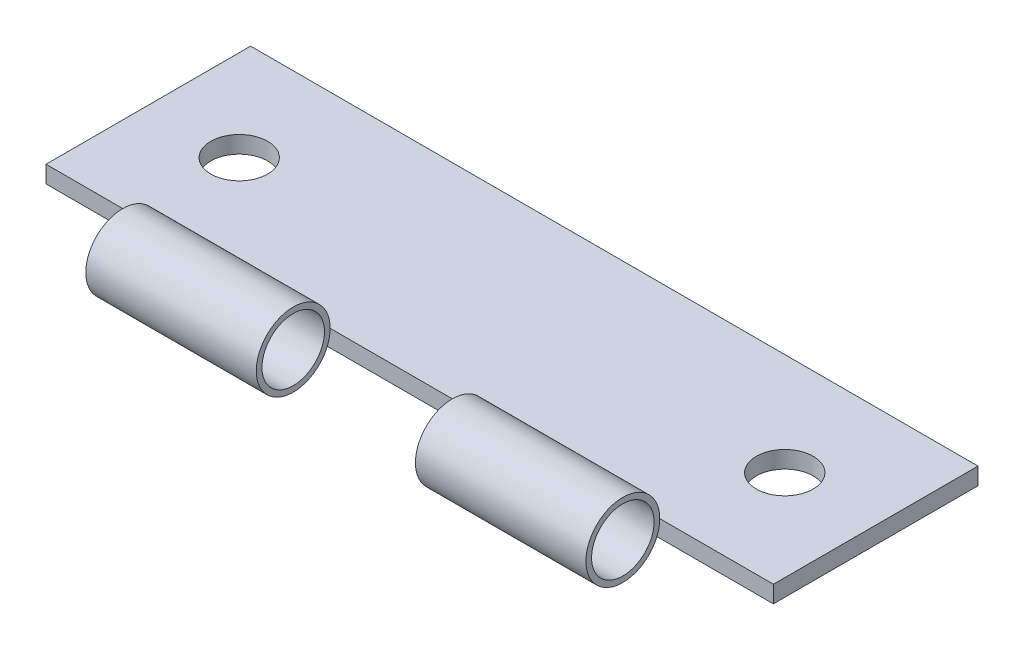
SolidWorks part; units mm, degrees
ref_plane "Front Plane" through (0, 0, 0) normal (0, 0, 1) x (1, 0, 0)
ref_plane "Top Plane" through (0, 0, 0) normal (0, 1, 0) x (1, 0, 0)
ref_plane "Right Plane" through (0, 0, 0) normal (1, 0, 0) x (0, 0, -1)
sketch "Sketch1" plane through (0, 0, 0) normal (0, 1, 0) x (1, 0, 0)
  line L1 (-32, 9) -> (32, 9)
  line L2 (-32, 9) -> (-32, -9)
  line L3 (-32, -9) -> (32, -9)
  line L4 (32, 9) -> (32, -9)
  line L5 (-32, 9) -> (32, -9) construction
  line L6 (-32, -9) -> (32, 9) construction
  point P0 (0, 0)
  dimension "D1" = 64
  dimension "D2" = 18
extrude "Boss-Extrude1" add sketch "Sketch1" along normal blind 1.5
sketch "Sketch2" plane through (0, 0, 0) normal (1, 0, 0) x (0, 0, -1)
  line L0 (-9, 1.5) -> (9, 1.5) construction
  line L1 (-9, 1.5) -> (-9, 0) construction
  circle A0 centre (-12.25, 1.5) radius 3.25
  dimension "D1" = 6.5
  dimension "D2" = 0
  dimension "D3" = 3.25
extrude "Boss-Extrude2" add sketch "Sketch2" along normal mid plane 64 separate body
sketch "Sketch3" plane through (0, 1.5, 0) normal (0, 1, 0) x (1, 0, 0)
  line L0 (-32, 9) -> (-32, -9) construction
  line L1 (32, -9) -> (32, 9) construction
  circle A0 centre (-24, 0) radius 2.5
  circle A1 centre (24, 0) radius 2.5
  dimension "D1" = 5
  dimension "D2" = 8
  dimension "D3" = 8
extrude "Cut-Extrude1" cut sketch "Sketch3" against normal blind 10
sketch "Sketch4" plane through (0, 0, 0) normal (0, 1, 0) x (1, 0, 0)
  line L0 (32, -9) -> (-32, -9) construction
  line L5 (-32, -15.5) -> (32, -15.5) construction
  line L22 (-32, -9) -> (-22, -9)
  line L23 (-32, -9) -> (-32, -15.5)
  line L24 (-32, -15.5) -> (-22, -15.5)
  line L25 (-22, -9) -> (-22, -15.5)
  line L26 (32, -9) -> (22, -9)
  line L27 (32, -9) -> (32, -15.5)
  line L28 (32, -15.5) -> (22, -15.5)
  line L29 (22, -9) -> (22, -15.5)
  line L30 (-7, -9) -> (7, -9)
  line L31 (-7, -9) -> (-7, -15.5)
  line L32 (-7, -15.5) -> (7, -15.5)
  line L33 (7, -9) -> (7, -15.5)
  dimension "D1" = 10
  dimension "D2" = 10
  dimension "D3" = 25
  dimension "D4" = 25
extrude "Cut-Extrude2" cut sketch "Sketch4" against normal blind 10 and the other way blind 10 contours L23 L22 L25 L24 | L31 L30 L33 L32 | L27 L26 L29 L28
sketch "Sketch5" plane through (22, 0, 0) normal (1, 0, 0) x (0, 0, -1)
  circle A0 centre (-12.25, 1.5) radius 2.75
  circle A1 centre (-12.25, 1.5) radius 3.25 construction
  dimension "D1" = 0.5
extrude "Cut-Extrude3" cut sketch "Sketch5" against normal blind 44
